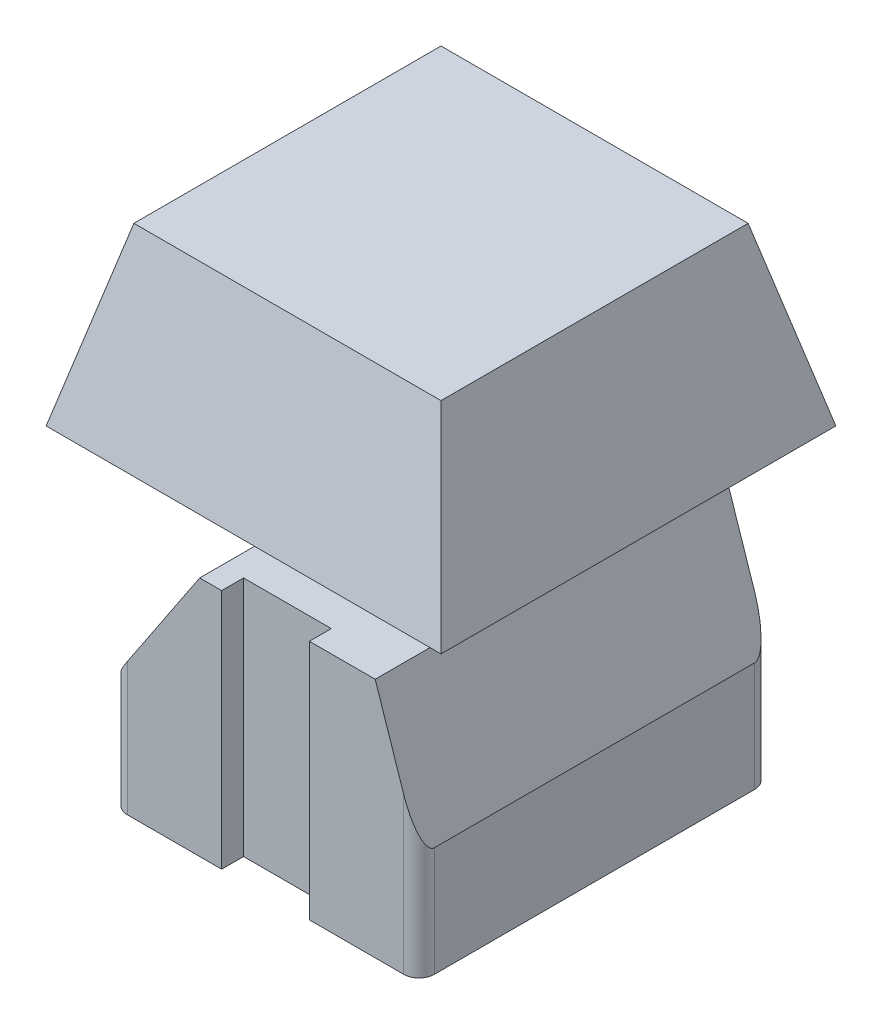
SolidWorks part; units mm, degrees
ref_plane "Front Plane" through (0, 0, 0) normal (0, 0, 1) x (1, 0, 0)
ref_plane "Top Plane" through (0, 0, 0) normal (0, 1, 0) x (1, 0, 0)
ref_plane "Right Plane" through (0, 0, 0) normal (1, 0, 0) x (0, 0, -1)
sketch "Sketch1" plane through (0, 0, 0) normal (0, 1, 0) x (1, 0, 0)
  line L0 (0, 7) -> (0, -7) construction
  line L1 (-6.3, -8) -> (-2, -8)
  line L2 (-7, -7.3) -> (-7, 7.3)
  line L3 (-6.3, 8) -> (-2, 8)
  line L4 (7, -7.3) -> (7, 7.3)
  line L5 (-6.8085, -7.7811) -> (6.8085, 7.7811) construction
  line L6 (-6.8085, 7.7811) -> (6.8085, -7.7811) construction
  line L7 (-2, 8) -> (-2, 7)
  line L8 (-2, 7) -> (2, 7)
  line L9 (2, 7) -> (2, 8)
  line L10 (2, 8) -> (6.3, 8)
  line L11 (2, -8) -> (2, -7)
  line L12 (2, -7) -> (-2, -7)
  line L13 (-2, -7) -> (-2, -8)
  line L14 (2, -8) -> (6.3, -8)
  arc A0 (6.3, -8) -> (7, -7.3) centre (6.3, -7.3) ccw
  arc A1 (7, 7.3) -> (6.3, 8) centre (6.3, 7.3) ccw
  arc A2 (-6.3, 8) -> (-7, 7.3) centre (-6.3, 7.3) ccw
  arc A3 (-7, -7.3) -> (-6.3, -8) centre (-6.3, -7.3) ccw
  point P0 (0, 0)
  dimension "D3" = 4
  dimension "D4" = 1
  dimension "D5" = 1
  dimension "D6" = 1
  dimension "D7" = 4
extrude "Boss-Extrude1" add sketch "Sketch1" along normal blind 11
sketch "Sketch2" plane through (0, 0, 8) normal (0, 0, 1) x (1, 0, 0)
  line L0 (-3, 11) -> (-7, 5)
  line L1 (-6.3, 11) -> (-2, 11) construction
  line L2 (-7, 11) -> (-7, 0) construction
  line L5 (-7, 5) -> (-7, 11)
  line L6 (-7, 11) -> (-3, 11)
extrude "Cut-Extrude1" cut sketch "Sketch2" against normal blind 18
sketch "Sketch3" plane through (0, 0, 8) normal (0, 0, 1) x (1, 0, 0)
  line L0 (5, 11) -> (7, 5)
  line L1 (2, 11) -> (6.3, 11) construction
  line L2 (7, 11) -> (7, 0) construction
  line L3 (5, 11) -> (7, 11)
  line L4 (7, 11) -> (7, 5)
  dimension "D1" = 2
  dimension "D2" = 6
extrude "Cut-Extrude2" cut sketch "Sketch3" against normal blind 18
sketch "Sketch4" plane through (0, 11, 0) normal (0, 1, 0) x (1, 0, 0)
  line L0 (0, 7) -> (0, 2) construction
  line L1 (2, 7) -> (-2, 7) construction
  line L2 (-2, -7) -> (2, -7) construction
  line L3 (-0.75, 0.75) -> (-0.75, 2)
  line L4 (-2, 0.75) -> (-0.75, 0.75)
  line L5 (-2, 0.75) -> (-2, -0.75)
  line L6 (-2, -0.75) -> (-0.75, -0.75)
  line L7 (2, 0.75) -> (2, -0.75)
  line L10 (0.75, -2) -> (-0.75, -2)
  line L11 (0.75, -2) -> (0.75, -0.75)
  line L12 (0.75, 2) -> (-0.75, 2)
  line L13 (-0.75, -2) -> (-0.75, -0.75)
  line L18 (0.75, 0.75) -> (2, 0.75)
  line L19 (0.75, 0.75) -> (0.75, 2)
  line L21 (0.75, -0.75) -> (2, -0.75)
  line L22 (0, -2) -> (0, -7) construction
  point P6 (0, 0)
  point P11 (0, 0)
  dimension "D1" = 4
  dimension "D2" = 4
  dimension "D3" = 1.5
  dimension "D4" = 1.5
extrude "Boss-Extrude2" add sketch "Sketch4" along normal blind 3.5
sketch "Sketch7" plane through (0, 14.5, 0) normal (0, 1, 0) x (1, 0, 0)
  line L0 (0, -9) -> (0, 9) construction
  line L1 (9, -9) -> (-9, -9)
  line L2 (-9, 0) -> (9, 0) construction
  line L3 (0, 9) -> (9, 9)
  line L4 (9, 9) -> (9, -9)
  line L5 (-9, -9) -> (-9, 9)
  line L6 (-9, 9) -> (0, 9)
  point P3 (0, 0)
  point P6 (0, 0)
  point P10 (0, 0)
  dimension "D1" = 18
  dimension "D2" = 18
extrude "Boss-Extrude3" add sketch "Sketch7" along normal blind 8
sketch "Sketch8" plane through (0, 0, -9) normal (0, 0, -1) x (-1, 0, 0)
  line L0 (9, 22.5) -> (7, 22.5)
  line L1 (-9, 22.5) -> (9, 22.5) construction
  line L2 (7, 22.5) -> (9, 14.5)
  line L3 (9, 14.5) -> (9, 22.5)
  line L4 (-9, 22.5) -> (-7, 22.5)
  line L5 (-7, 22.5) -> (-9, 14.5)
  line L6 (-9, 14.5) -> (-9, 22.5)
  dimension "D1" = 2
  dimension "D2" = 2
sketch "Sketch10" plane through (-9, 0, 0) normal (-1, 0, 0) x (0, 0, 1)
  line L0 (-9, 22.5) -> (-7, 22.5)
  line L1 (-9, 22.5) -> (9, 22.5) construction
  line L2 (-7, 22.5) -> (-9, 14.5)
  line L3 (-9, 14.5) -> (-9, 22.5)
  line L4 (7, 22.5) -> (9, 22.5)
  line L5 (9, 22.5) -> (9, 14.5)
  line L6 (9, 14.5) -> (7, 22.5)
  dimension "D1" = 2
  dimension "D2" = 2
extrude "Cut-Extrude4" cut sketch "Sketch10" against normal blind 27
extrude "Cut-Extrude5" cut sketch "Sketch8" against normal blind 27
sketch "Sketch11" plane through (-7, 0, 0) normal (-1, 0, 0) x (0, 0, 1)
  line L0 (-7.3, 5) -> (7.3, 5)
  line L1 (7.3, 5) -> (7.3, 4.9)
  line L2 (7.3, 5) -> (7.3, 0) construction
  line L3 (7.3, 4.9) -> (-7.3, 4.9)
  line L4 (-7.3, 5) -> (-7.3, 0) construction
  line L5 (-7.3, 4.9) -> (-7.3, 5)
  dimension "D1" = 0.1
extrude "Boss-Extrude4" add sketch "Sketch11" along normal blind 0.1
